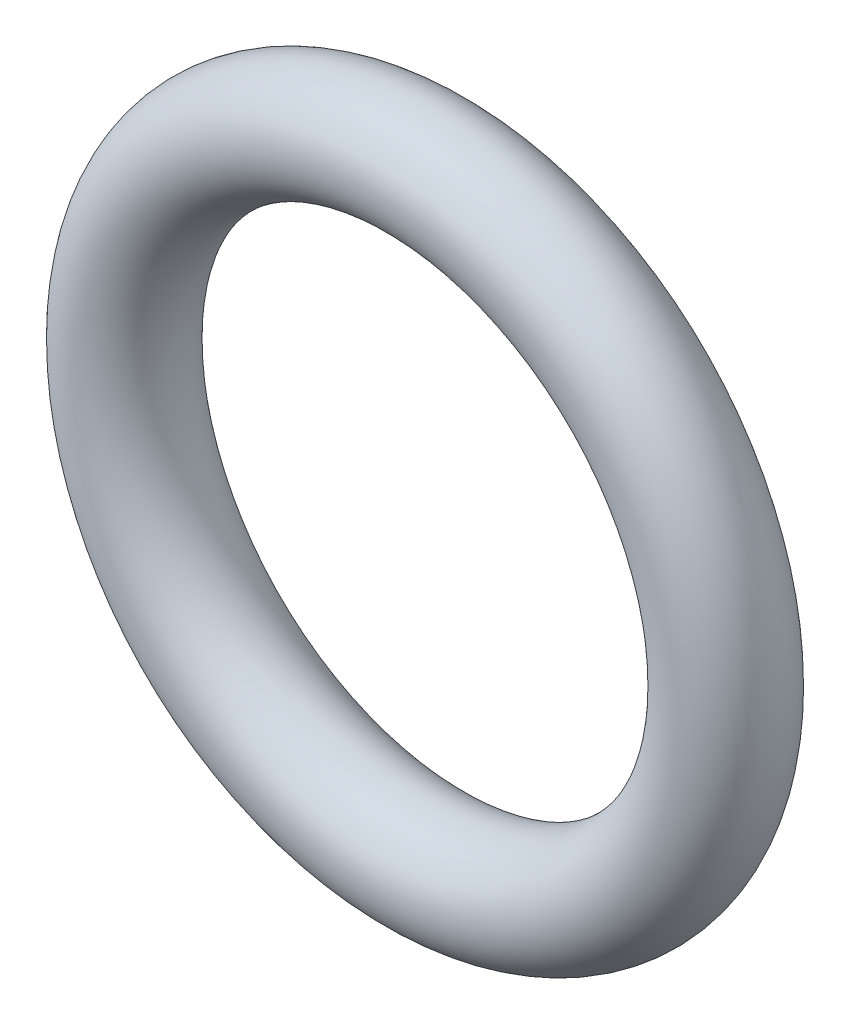
SolidWorks part; units mm, degrees
ref_plane "Front" through (0, 0, 0) normal (0, 0, 1) x (1, 0, 0)
ref_plane "Top" through (0, 0, 0) normal (0, 1, 0) x (1, 0, 0)
ref_plane "Right" through (0, 0, 0) normal (1, 0, 0) x (0, 0, -1)
sketch "Sketch1" plane through (0, 0, 0) normal (0, 0, 1) x (1, 0, 0)
  circle A0 centre (0, 0) radius 4.8578
  dimension "D1" = 9.7155
sketch "Sketch2" plane through (0, 0, 0) normal (0, 1, 0) x (1, 0, 0)
  circle A0 centre (4.8578, 0) radius 0.889
  dimension "D1" = 1.778
sweep "Base-Sweep" add profiles "Sketch2" path "Sketch1"
ref_plane "Plane1" through (0, 0, -0.889) normal (0, 0, 1) x (1, 0, 0)
ref_plane "Plane2" through (0, 0, 0.889) normal (0, 0, 1) x (1, 0, 0)
